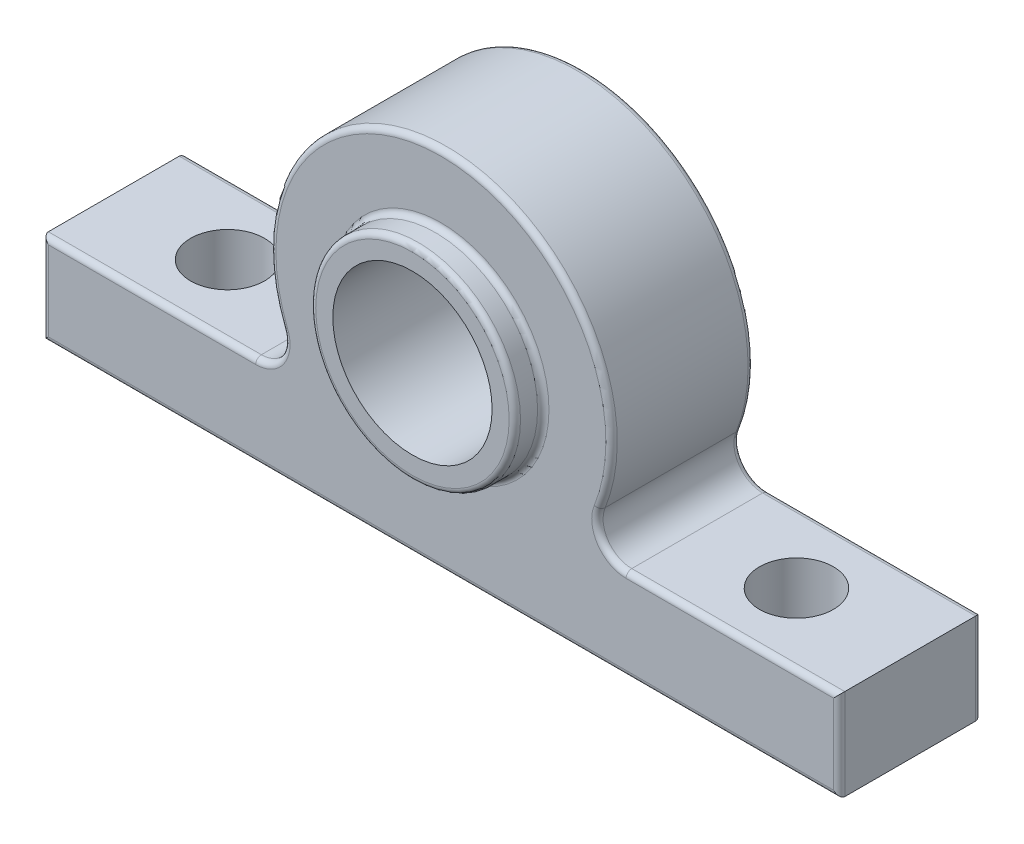
SolidWorks part; units mm, degrees
ref_plane "Спереди" through (0, 0, 0) normal (0, 0, 1) x (1, 0, 0)
ref_plane "Сверху" through (0, 0, 0) normal (0, 1, 0) x (1, 0, 0)
ref_plane "Справа" through (0, 0, 0) normal (1, 0, 0) x (0, 0, -1)
sketch "Эскиз1" plane through (0, 0, 0) normal (0, 0, 1) x (1, 0, 0)
  line L0 (-70, 16) -> (-70, 0)
  line L1 (70, 0) -> (70, 16)
  line L2 (-70, 0) -> (70, 0)
  line L3 (-70, 16) -> (-32.5538, 16)
  line L4 (32.5538, 16) -> (70, 16)
  line L5 (27.7836, 22.8517) -> (27.9756, 22.8517)
  line L6 (-27.7836, 22.8517) -> (-27.9756, 22.8517)
  circle A0 centre (0, 34) radius 14
  arc A1 (27.8517, 22.8517) -> (-27.8517, 22.8517) centre (0, 34) ccw
  arc A2 (27.8927, 22.9547) -> (32.5538, 16) centre (32.5538, 21.0393) ccw
  arc A3 (-32.5538, 16) -> (-27.8927, 22.9547) centre (-32.5538, 21.0393) ccw
extrude "Бобышка-Вытянуть1" add sketch "Эскиз1" along normal blind 25
sketch "Эскиз2" plane through (0, 0, 25) normal (0, 0, 1) x (1, 0, 0)
  circle A0 centre (0, 33.8927) radius 18
extrude "Вырез-Вытянуть1" cut sketch "Эскиз2" against normal blind 5
sketch "Эскиз3" plane through (0, 0, 0) normal (0, 0, -1) x (-1, 0, 0)
  circle A0 centre (0, 34) radius 18
extrude "Вырез-Вытянуть2" cut sketch "Эскиз3" against normal blind 5
sketch "Эскиз4" plane through (0, 0, 20) normal (0, 0, 1) x (1, 0, 0)
  circle A0 centre (0, 34) radius 14
  circle A1 centre (0, 33.8927) radius 18
extrude "Бобышка-Вытянуть2" add sketch "Эскиз4" along normal blind 10
fillet "Скругление2" radius 1 1 edges at (18, 33.8927, 30)
sketch "Эскиз5" plane through (0, 0, 5) normal (0, 0, -1) x (-1, 0, 0)
  circle A0 centre (0, 34) radius 14
  circle A1 centre (0, 34) radius 18
extrude "Бобышка-Вытянуть3" add sketch "Эскиз5" along normal blind 10
fillet "Скругление3" radius 1 1 edges at (-18, 34, -5)
sketch "Эскиз6" plane through (0, 16, 0) normal (0, 1, 0) x (1, 0, 0)
  line L0 (70, -25) -> (70, 0) construction
  line L2 (32.5538, -25) -> (70, -25) construction
  line L3 (-70, -25) -> (-70, 0) construction
  line L5 (-70, 0) -> (-32.5538, 0) construction
  circle A0 centre (50, -12.5) radius 6.5
  circle A1 centre (-50, -12.5) radius 6.5
  point P4 (51.2769, -25)
  point P13 (-59.6142, 0)
  dimension "D3" = 13
  dimension "D4" = 13
  dimension "D1" = 20
  dimension "D2" = 12.5
  dimension "D5" = 20
  dimension "D6" = 12.5
extrude "Вырез-Вытянуть3" cut sketch "Эскиз6" against normal blind 16
fillet "Скругление4" radius 1 9 edges at (0, 64, 25) (28.3677, 18.2337, 25) (51.2769, 16, 25) (70, 8, 25) (0, 0, 25) (-70, 8, 25) (-51.2769, 16, 25) (-28.3677, 18.2337, 25) (18, 33.8927, 25)
fillet "Скругление5" radius 1 9 edges at (-51.2769, 16, 0) (-70, 8, 0) (0, 0, 0) (70, 8, 0) (51.2769, 16, 0) (28.3677, 18.2337, 0) (0, 64, 0) (-28.3677, 18.2337, 0) (-18, 34, 0)
